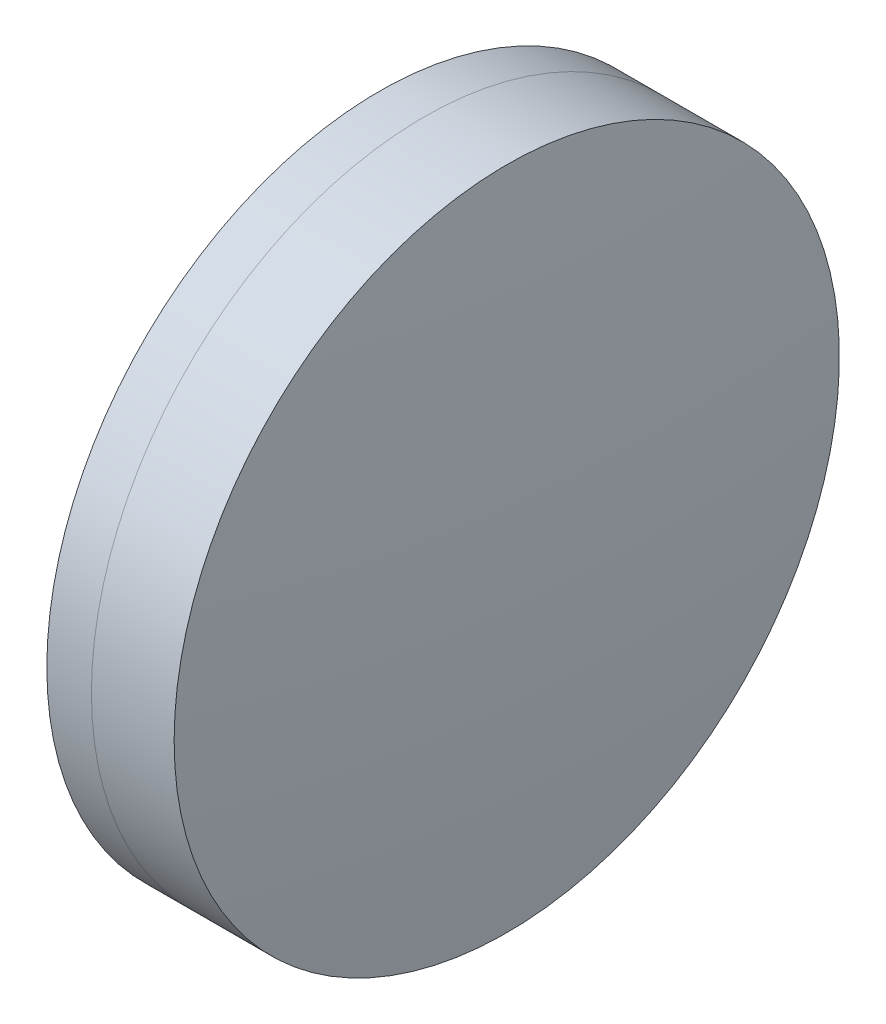
SolidWorks part; units mm, degrees
ref_plane "前视基准面" through (0, 0, 0) normal (0, 0, 1) x (1, 0, 0)
ref_plane "上视基准面" through (0, 0, 0) normal (0, 1, 0) x (1, 0, 0)
ref_plane "右视基准面" through (0, 0, 0) normal (1, 0, 0) x (0, 0, -1)
sketch "草图1" plane through (0, 0, 0) normal (0, 1, 0) x (1, 0, 0)
  line L0 (124.5233, 0) -> (395.1269, 0) construction
  line L1 (329.9294, -25.4) -> (333.3352, -25.4)
  line L2 (329.9294, 25.4) -> (333.3352, 25.4)
  arc A0 (333.3352, -25.4) -> (333.3352, 25.4) centre (265.8575, 0) ccw
  arc A1 (329.9294, 25.4) -> (329.9294, -25.4) centre (409.1575, 0) ccw
  point P10 (325.9575, 0)
  point P11 (337.9575, 0)
  dimension "D3" = 83.2
  dimension "D4" = 72.1
  dimension "D1" = 25.4
  dimension "D2" = 25.4
  dimension "D5" = 12
revolve "旋转1" add sketch "草图1" angle 360 about L0
sketch "草图2" plane through (0, 0, 0) normal (0, 1, 0) x (1, 0, 0)
  line L0 (-0.5519, 0) -> (409.4962, 0) construction
  line L2 (333.3352, 25.4) -> (339.6517, 25.4)
  line L3 (333.3352, -25.4) -> (339.6517, -25.4)
  arc A0 (339.6517, -25.4) -> (339.6517, 25.4) centre (93.2575, 0) ccw
  arc A1 (333.3352, -25.4) -> (333.3352, 25.4) centre (265.8575, 0) ccw construction
  arc A2 (333.3352, -25.4) -> (333.3352, 25.4) centre (265.8575, 0) ccw
  point P4 (337.9575, 0)
  point P8 (340.9575, 0)
  dimension "D1" = 247.7
  dimension "D2" = 3
revolve "旋转3" add sketch "草图2" angle 360 about L0
